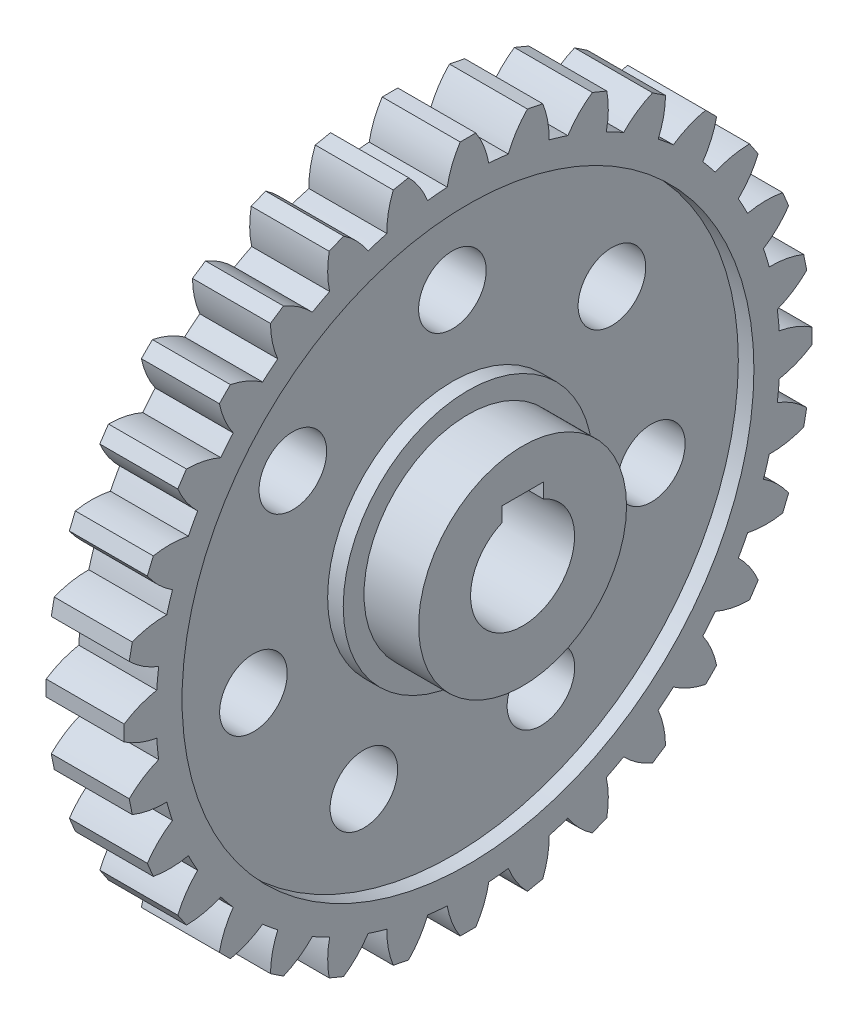
SolidWorks part; units mm, degrees
ref_plane "Front Plane" through (0, 0, 0) normal (0, 0, 1) x (1, 0, 0)
ref_plane "Top Plane" through (0, 0, 0) normal (0, 1, 0) x (1, 0, 0)
ref_plane "Right Plane" through (0, 0, 0) normal (1, 0, 0) x (0, 0, -1)
sketch "Sketch1" plane through (0, 0, 0) normal (1, 0, 0) x (0, 0, -1)
  circle A0 centre (0, 0) radius 60
  dimension "D1" = 120
extrude "Boss-Extrude1" add sketch "Sketch1" along normal mid plane 15
sketch "Sketch2" plane through (7.5, 0, 0) normal (1, 0, 0) x (0, 0, -1)
  line L0 (0, 0) -> (0, 95.4773) construction
  line L1 (-1.5, 66.1365) -> (1.5, 66.1365)
  arc A0 (-4, 59.8665) -> (4, 59.8665) centre (0, 0) cw
  circle A1 centre (0, 0) radius 60 construction
  arc A2 (-4, 59.8665) -> (-1.5, 66.1365) centre (12.7267, 56.8306) cw
  arc A3 (4, 59.8665) -> (1.5, 66.1365) centre (-12.7267, 56.8306) ccw
  point P8 (0, 66.1365)
  point P9 (0, 60)
  dimension "D4" = 17
  dimension "D1" = 1.5
  dimension "D2" = 6.27
  dimension "D3" = 4
extrude "Boss-Extrude2" add sketch "Sketch2" against normal up to surface (15 mm away) contours A3 A0 A2 L1 up to face at (-7.5, 0, -60)
sketch "Sketch5" plane through (0, 0, 0) normal (1, 0, 0) x (0, 0, -1)
  circle A0 centre (0, 0) radius 20
  dimension "D1" = 40
extrude "Boss-Extrude5" add sketch "Sketch5" along normal mid plane 36
sketch "Sketch6" plane through (18, 0, 0) normal (1, 0, 0) x (0, 0, -1)
  line L0 (0, 0) -> (0, 12) construction
  line L1 (-4, 12) -> (4, 12)
  line L2 (-4, 12) -> (-4, 9.1652)
  line L3 (4, 12) -> (4, 9.1652)
  arc A0 (-4, 9.1652) -> (4, 9.1652) centre (0, 0) ccw
  dimension "D1" = 20
  dimension "D2" = 8
  dimension "D3" = 12
extrude "Cut-Extrude1" cut sketch "Sketch6" against normal through all
sketch "Sketch7" plane through (7.5, 0, 0) normal (1, 0, 0) x (0, 0, -1)
  circle A0 centre (0, 0) radius 55
  circle A1 centre (0, 0) radius 24
  dimension "D1" = 110
  dimension "D2" = 48
extrude "Cut-Extrude2" cut sketch "Sketch7" against normal blind 3
sketch "Sketch8" plane through (4.5, 0, 0) normal (1, 0, 0) x (0, 0, -1)
  circle A0 centre (0, 0) radius 39.25 construction
  circle A1 centre (0, 39.25) radius 6.5
  circle A2 centre (30.6869, 24.472) radius 6.5
  circle A3 centre (38.2659, -8.7339) radius 6.5
  circle A4 centre (17.0299, -35.363) radius 6.5
  circle A5 centre (-17.0299, -35.363) radius 6.5
  circle A6 centre (-38.2659, -8.7339) radius 6.5
  circle A7 centre (-30.6869, 24.472) radius 6.5
  point P19 (0, 0)
  dimension "D1" = 78.5
  dimension "D2" = 13
  dimension "D3" = 7
extrude "Cut-Extrude3" cut sketch "Sketch8" against normal through all
pattern_circular "CirPattern2" count 32 over 360 about axis through (0, 0, 0) along (1, 0, 0) of "Boss-Extrude2"
